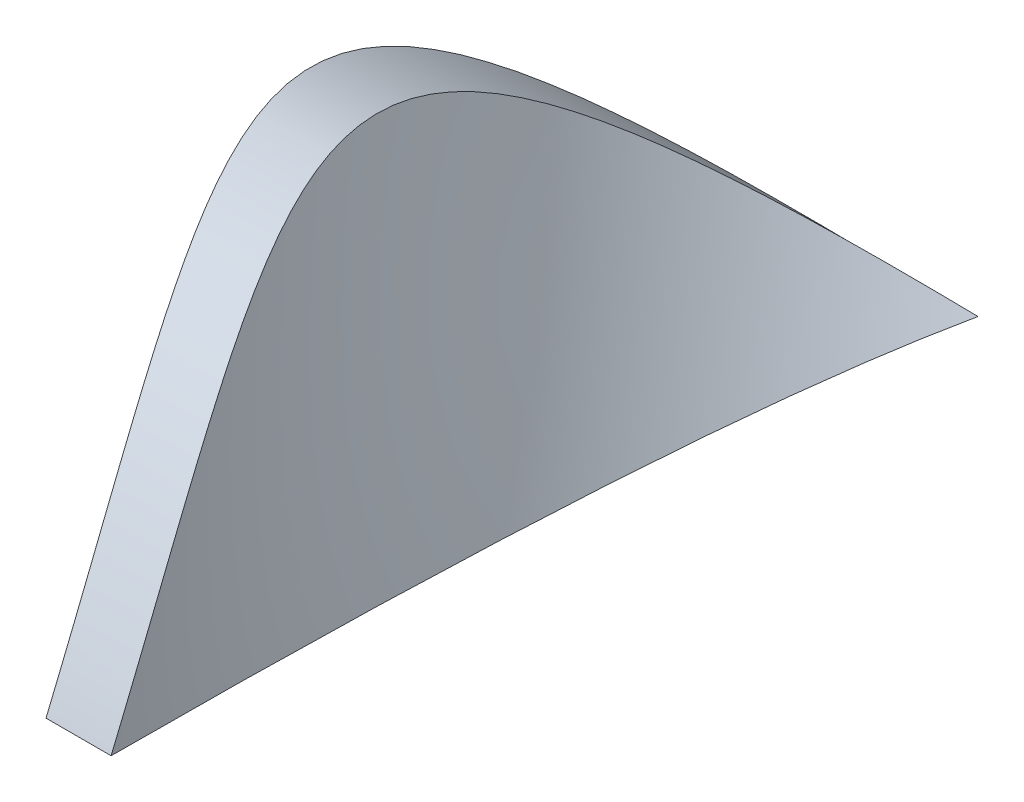
SolidWorks part; units mm, degrees
material "外包尼龙打印"
ref_plane "前视基准面" through (0, 0, 0) normal (0, 0, 1) x (1, 0, 0)
ref_plane "上视基准面" through (0, 0, 0) normal (0, 1, 0) x (1, 0, 0)
ref_plane "右视基准面" through (0, 0, 0) normal (1, 0, 0) x (0, 0, -1)
sketch "草图1" plane through (0, 0, 0) normal (0, 0, 1) x (1, 0, 0)
  circle A0 centre (0, 0) radius 2.5
  dimension "D1" = 5
curve "螺旋线/涡状线1" pitch 330 height 60 turns 0.1818
sketch "草图3" plane through (0, 0, 0) normal (0, 0, 1) x (1, 0, 0)
  line L1 (0.5, -23) -> (4.5, -23)
  line L2 (0.5, -23) -> (0.5, 23)
  line L3 (0.5, 23) -> (4.5, 23)
  line L4 (4.5, -23) -> (4.5, 23)
  line L5 (0.5, -23) -> (4.5, 23) construction
  line L6 (0.5, 23) -> (4.5, -23) construction
  spline S0 degree 3 poles (2.5, 0) (2.5, 0.1904) (2.4563, 0.5712) (2.2631, 1.1127) (1.9523, 1.5964) (1.54, 1.9971) (1.2117, 2.195) (1.0385, 2.2741) knots 0 0 0 0 0.2 0.4 0.6 0.8 1 1 1 1 construction
  point P0 (2.5, 0)
  point P1 (2.5, 0)
  dimension "D1" = 46
  dimension "D2" = 4
sweep "扫描1" add profiles "草图3" path "螺旋线/涡状线1"
sketch "草图5" plane through (0, 0, 0) normal (1, 0, 0) x (0, 0, -1)
  line L0 (-731.2271, 0) -> (49268.7723, 0) construction
  line L1 (0, -1000) -> (0, 49000) construction
  line L2 (50, 0) -> (145.7177, 0)
  line L3 (145.7177, 0) -> (145.7177, 81.7667)
  line L4 (145.7177, 81.7667) -> (-35.1819, 81.7667)
  line L5 (-35.1819, 81.7667) -> (-35.1819, 0)
  line L6 (-35.1819, 0) -> (0, 0)
  spline S0 degree 2 poles (50, 0) (15.153, 36.373) (0, 0) knots 0 0 0 1 1 1
  point P6 (12, 16)
  dimension "D1" = 50
  dimension "D2" = 16
  dimension "D3" = 12
extrude "切除-拉伸1" cut sketch "草图5" against normal mid plane 42
sketch "草图6" plane through (0, 0, 0) normal (1, 0, 0) x (0, 0, -1)
  line L0 (-1000, 0) -> (49000, 0) construction
  line L1 (0, -1000) -> (0, 49000) construction
  line L2 (0, 0) -> (71.6279, 0)
  line L3 (27.5565, -66.0674) -> (-48.8248, -55.1961)
  line L4 (-48.8248, -55.1961) -> (0, 0)
  arc A0 (71.6279, 0) -> (27.5565, -66.0674) centre (0.0714, 0) cw
  dimension "D1" = 0
extrude "切除-拉伸2" cut sketch "草图6" against normal mid plane 197
sketch "草图7" plane through (0, 0, 0) normal (0, 0, 1) x (1, 0, 0)
  circle A1 centre (0, 0) radius 2.5
  circle A2 centre (0, 0) radius 2.5
  dimension "D1" = 0
ref_plane "基准面1" through (10, 0, 0) normal (1, 0, 0) x (0, 0, -1)
